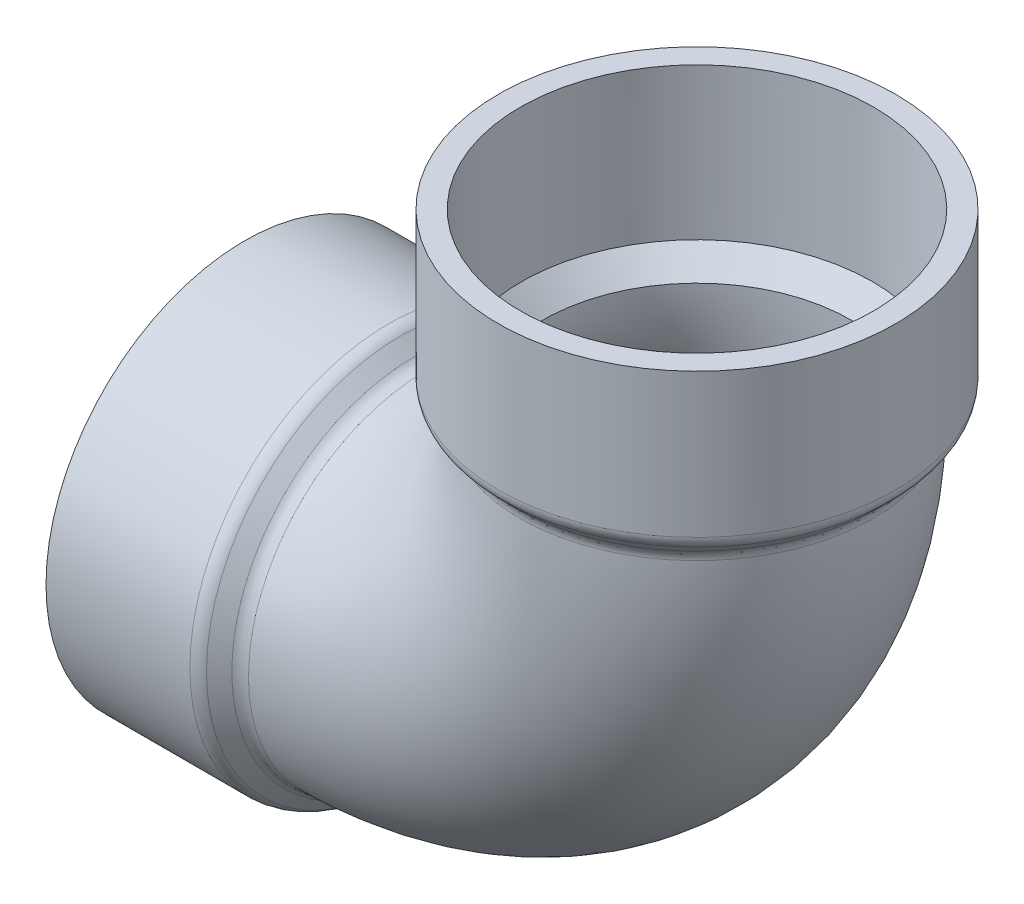
SolidWorks part; units mm, degrees
ref_plane "Front Plane" through (0, 0, 0) normal (0, 0, 1) x (1, 0, 0)
ref_plane "Top Plane" through (0, 0, 0) normal (0, 1, 0) x (1, 0, 0)
ref_plane "Right Plane" through (0, 0, 0) normal (1, 0, 0) x (0, 0, -1)
sketch "Sketch0" plane through (0, 0, 0) normal (0, 0, 1) x (1, 0, 0)
  line L0 (-114.3, 0) -> (0, 0) construction
  line L1 (0, 0) -> (0, 114.3) construction
  line L2 (-76.2, 0) -> (0, 0) construction
  line L3 (0, 0) -> (0, 76.2) construction
  line L4 (-114.3, 50.2285) -> (-114.3, -50.2285) construction
  line L5 (-76.2, 44.3865) -> (-114.3, 44.6405) construction
  line L6 (-76.2, 44.3865) -> (-76.2, -44.3865) construction
  line L7 (-76.2, -44.3865) -> (-114.3, -44.6405) construction
  line L8 (-114.3, 44.6405) -> (-114.3, -44.6405) construction
  line L9 (-50.2285, 114.3) -> (50.2285, 114.3) construction
  line L10 (-44.6405, 114.3) -> (44.6405, 114.3) construction
  line L11 (44.6405, 114.3) -> (44.3865, 76.2) construction
  line L12 (44.3865, 76.2) -> (-44.3865, 76.2) construction
  line L13 (-44.3865, 76.2) -> (-44.6405, 114.3) construction
  line L14 (-76.2, 38.9636) -> (-76.2, -38.9636) construction
  line L15 (-76.2, -38.9636) -> (-76.2, -44.5516) construction
  line L16 (-114.3, -44.6405) -> (-114.3, -50.2285) construction
  line L17 (38.9636, 76.2) -> (44.5516, 76.2) construction
  line L18 (-38.9636, 76.2) -> (38.9636, 76.2) construction
  line L19 (44.6405, 114.3) -> (50.2285, 114.3) construction
sketch "Sketch1" plane through (0, 0, 0) normal (0, 0, 1) x (1, 0, 0)
  line L0 (-114.3, 0) -> (0, 0) construction
  line L1 (-114.3, 0) -> (0, 0) construction
  line L2 (-76.2, -50.2285) -> (-70.5231, -44.5516)
  line L3 (-114.3, -50.2285) -> (-76.2, -50.2285)
  line L4 (-114.3, -50.2285) -> (-114.3, -44.6405)
  line L5 (-114.3, -44.6405) -> (-76.2, -44.3865)
  line L6 (-76.2, -50.2285) -> (-76.2, -44.3865) construction
  line L7 (-70.5231, -44.5516) -> (-70.5231, -38.9636)
  line L8 (-70.5231, -38.9636) -> (-76.2, -44.3865)
  line L9 (-76.2, -50.2285) -> (-70.5231, -50.2285) construction
  line L10 (-76.2, -38.9636) -> (-70.5231, -38.9636) construction
  line L11 (-70.5231, -50.2285) -> (-70.5231, -44.5516) construction
  line L12 (-76.2, -44.5516) -> (-70.5231, -44.5516) construction
revolve "Revolve1" add sketch "Sketch1" angle 360 about L1
sketch "Sketch2" plane through (0, 0, 0) normal (0, 0, 1) x (1, 0, 0)
  line L0 (44.6405, 114.3) -> (44.3865, 76.2)
  line L1 (44.3865, 76.2) -> (50.2285, 76.2) construction
  line L2 (50.2285, 76.2) -> (50.2285, 114.3)
  line L3 (50.2285, 114.3) -> (44.6405, 114.3)
  line L4 (0, 0) -> (0, 114.3) construction
  line L5 (0, 0) -> (0, 114.3) construction
  line L6 (44.3865, 76.2) -> (38.9636, 70.5231)
  line L7 (38.9636, 76.2) -> (38.9636, 70.5231) construction
  line L8 (50.2285, 76.2) -> (44.5516, 70.5231)
  line L9 (44.5516, 70.5231) -> (38.9636, 70.5231)
  line L10 (50.2285, 76.2) -> (50.2285, 70.5231) construction
  line L11 (50.2285, 70.5231) -> (44.5516, 70.5231) construction
  line L12 (44.5516, 76.2) -> (44.5516, 70.5231) construction
revolve "Revolve2" add sketch "Sketch2" angle 360 about L5
sketch "Sketch3" plane through (-70.5231, 0, 0) normal (1, 0, 0) x (0, 0, -1)
  circle A0 centre (0, 0) radius 38.9636
  circle A1 centre (0, 0) radius 44.5516
sketch "Sketch4" plane through (0, 0, 0) normal (0, 0, 1) x (1, 0, 0)
  line L0 (-114.3, 0) -> (0, 0) construction
  line L1 (0, 0) -> (0, 114.3) construction
  line L2 (-114.3, 0) -> (-70.5231, 0) construction
  line L3 (0, 70.5231) -> (0, 114.3) construction
  line L4 (-70.5231, -44.5516) -> (-70.5231, 44.5516) construction
  arc A0 (-70.5231, 0) -> (0, 70.5231) centre (-70.5231, 70.5231) ccw
sweep "Sweep1" add profiles "Sketch3" path "Sketch4"
fillet "Fillet1" radius 4.191 4 edges at (-70.5231, 0, -44.5516) (0, 70.5231, -44.5516) (0, 76.2, -50.2285) (-76.2, 0, 50.2285)
equation "\"D1@Fillet1\" = \"H@Sketch0\" * 3 / 4"
